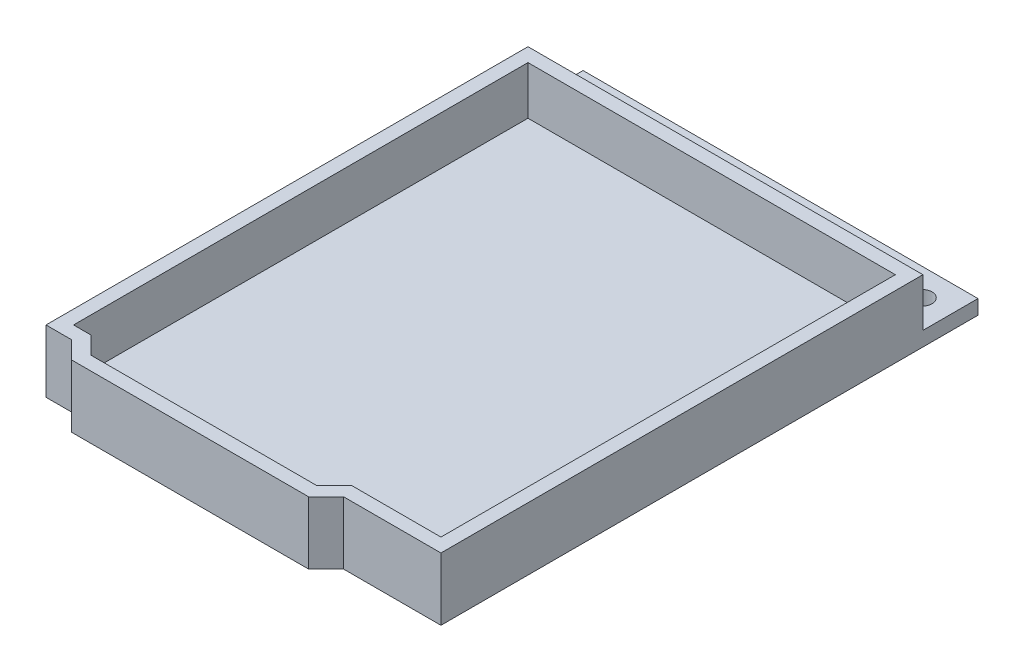
SolidWorks part; units mm, degrees
ref_plane "Front Plane" through (0, 0, 0) normal (0, 0, 1) x (1, 0, 0)
ref_plane "Top Plane" through (0, 0, 0) normal (0, 1, 0) x (1, 0, 0)
ref_plane "Right Plane" through (0, 0, 0) normal (1, 0, 0) x (0, 0, -1)
sketch "Sketch1" plane through (0, 0, 0) normal (0, 1, 0) x (1, 0, 0)
  line L0 (28.68, 0) -> (28.68, -8)
  line L1 (28.68, 0) -> (-28.68, 0)
  line L2 (28.68, -8) -> (28.68, -78)
  line L3 (28.68, -78) -> (-28.68, -78)
  line L4 (-28.68, -78) -> (-28.68, 0)
extrude "Boss-Extrude1" add sketch "Sketch1" along normal blind 2.1
sketch "Sketch2" plane through (0, 2.1, 0) normal (0, 1, 0) x (1, 0, 0)
  line L1 (28.68, -78) -> (28.68, 0) construction
  line L2 (28.68, -8) -> (-28.68, -8)
  line L3 (-28.68, 0) -> (-28.68, -78) construction
  line L4 (-28.68, -8) -> (-28.68, -78)
  line L5 (-28.68, -78) -> (28.68, -78)
  line L6 (28.68, -78) -> (28.68, -8)
extrude "Boss-Extrude2" add sketch "Sketch2" along normal blind 7
sketch "Sketch3" plane through (0, 9.1, 0) normal (0, 1, 0) x (1, 0, 0)
  line L7 (-26.68, -10) -> (26.68, -10)
  line L8 (-26.68, -10) -> (-26.68, -76)
  line L9 (-26.68, -76) -> (26.68, -76)
  line L10 (26.68, -10) -> (26.68, -76)
extrude "Cut-Extrude1" cut sketch "Sketch3" against normal blind 7
sketch "Sketch4" plane through (0, 2.1, 0) normal (0, 1, 0) x (1, 0, 0)
  circle A2 centre (24.5, -4) radius 1.5
  circle A3 centre (-24.5, -4) radius 1.5
extrude "Cut-Extrude2" cut sketch "Sketch4" against normal up to surface (2.1 mm away) up to face at (0, 0, 39)
sketch "Sketch5" plane through (0, 9.1, 0) normal (0, 1, 0) x (1, 0, 0)
  line L0 (-26.68, -76) -> (-24.14, -76)
  line L1 (-26.68, -76) -> (26.68, -76) construction
  line L3 (-28.68, -78) -> (28.68, -78) construction
  line L4 (-21.6, -78.54) -> (11.17, -78.54)
  line L9 (-26.68, -76) -> (-26.68, -78)
  line L17 (-21.6, -78.54) -> (-24.14, -76)
  line L19 (-24.9684, -78) -> (-22.4284, -80.54)
  line L20 (-26.68, -78) -> (-24.9684, -78)
  line L21 (14.5384, -78) -> (11.9984, -80.54)
  line L24 (13.71, -76) -> (11.17, -78.54)
  line L25 (-22.4284, -80.54) -> (11.9984, -80.54)
  line L26 (14.5384, -78) -> (14.5384, -76)
  line L27 (14.5384, -76) -> (13.71, -76)
sketch "Sketch6" plane through (0, 9.1, 0) normal (0, 1, 0) x (1, 0, 0)
  line L4 (-26.68, -76) -> (-26.68, -78)
  line L5 (-26.68, -78) -> (13.71, -78)
  line L6 (13.71, -78) -> (13.71, -76)
  line L7 (13.71, -76) -> (-26.68, -76)
extrude "Cut-Extrude3" cut sketch "Sketch6" against normal up to surface (9.1 mm away) up to face at (24.5, 0, 2.5)
extrude "Boss-Extrude3" add sketch "Sketch5" against normal up to surface (9.1 mm away) up to face at (-3.2425, 0, 58)
sketch "Sketch7" plane through (0, 0, 0) normal (0, -1, 0) x (1, 0, 0)
  line L0 (13.71, 76) -> (-24.14, 76)
  line L1 (-24.14, 76) -> (-21.6, 78.54)
  line L2 (-21.6, 78.54) -> (11.17, 78.54)
  line L3 (11.17, 78.54) -> (13.71, 76)
extrude "Boss-Extrude4" add sketch "Sketch7" against normal up to surface (2.1 mm away) up to face at (-1.7383, 2.1, 54)
